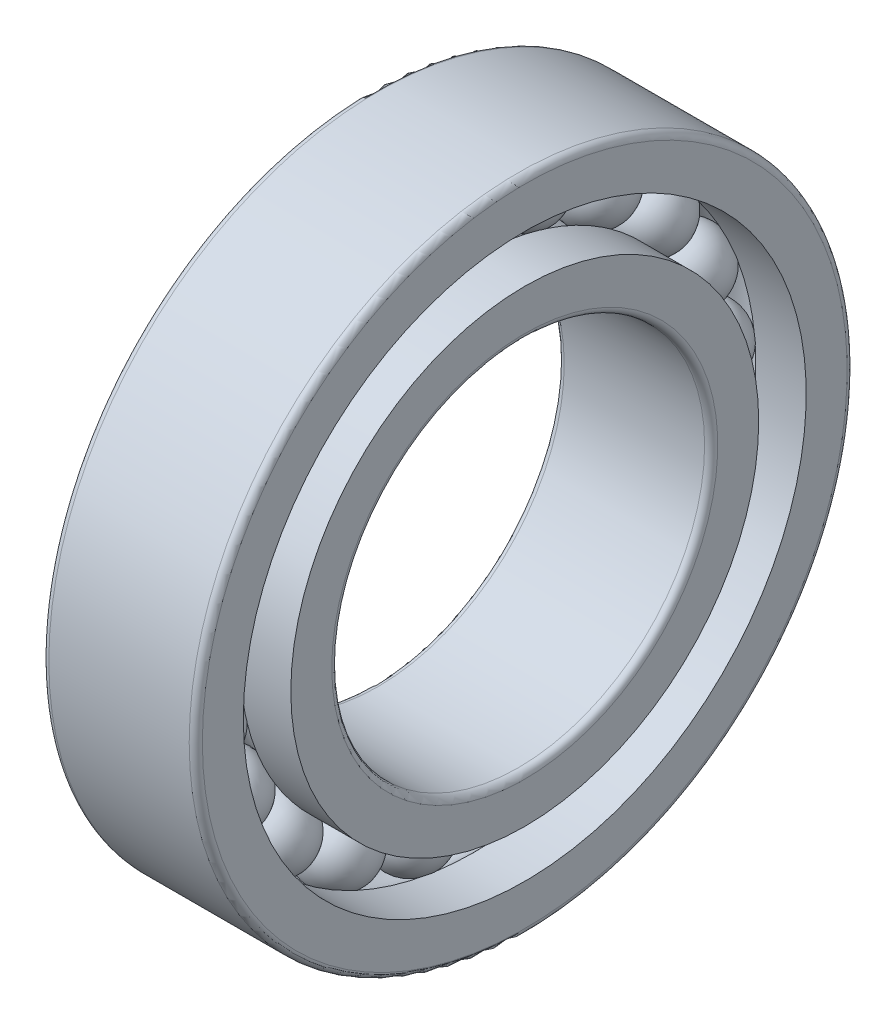
SolidWorks part; units mm, degrees
ref_plane "Front" through (0, 0, 0) normal (0, 0, 1) x (1, 0, 0)
ref_plane "Top" through (0, 0, 0) normal (0, 1, 0) x (1, 0, 0)
ref_plane "Right" through (0, 0, 0) normal (1, 0, 0) x (0, 0, -1)
sketch "Sketch1" plane through (0, 0, 0) normal (0, 0, 1) x (1, 0, 0)
  line L0 (-9.6833, 0) -> (9.8371, 0) construction
  line L1 (-1.625, 11.75) -> (1.625, 11.75)
  line L2 (-4.5966, 11.75) -> (4.6657, 11.75) construction
  arc A0 (1.625, 11.75) -> (-1.625, 11.75) centre (0, 11.75) ccw
revolve "Revolve1" add sketch "Sketch1" angle 360 about L2
sketch "Sketch2" plane through (0, 0, 0) normal (0, 0, 1) x (1, 0, 0)
  line L0 (-3.5, 10.6667) -> (-3.5, 8.5)
  line L1 (-3.5, 8.5) -> (3.5, 8.5)
  line L2 (3.5, 8.5) -> (3.5, 10.6667)
  line L3 (3.5, 10.6667) -> (1.1978, 10.6667)
  line L4 (-6.9714, 0) -> (8.1665, 0) construction
  line L5 (-6.7058, 11.75) -> (6.7058, 11.75) construction
  line L6 (-1.1978, 10.6667) -> (-3.5, 10.6667)
  arc A0 (-1.1978, 10.6667) -> (1.1978, 10.6667) centre (0, 11.75) ccw
revolve "Revolve2" add sketch "Sketch2" angle 360 about L4
sketch "Sketch3" plane through (0, 0, 0) normal (0, 0, 1) x (1, 0, 0)
  line L0 (-8.7107, 0) -> (9.1288, 0) construction
  line L1 (-3.5, 15) -> (3.5, 15)
  line L2 (-3.5, 15) -> (-3.5, 12.8333)
  line L3 (-3.5, 12.8333) -> (-1.1978, 12.8333)
  line L4 (3.5, 15) -> (3.5, 12.8333)
  line L5 (-7.2948, 11.75) -> (7.2948, 11.75) construction
  line L6 (1.1978, 12.8333) -> (3.5, 12.8333)
  arc A0 (1.1978, 12.8333) -> (-1.1978, 12.8333) centre (0, 11.75) ccw
revolve "Revolve3" add sketch "Sketch3" angle 360 about L0
pattern_circular "Circular-Pattern1" count 21 over 360 about axis through (0, 0, 0) along (1, 0, 0) of "Revolve1"
fillet "Fillet1" radius 0.3 4 edges at (-3.5, 0, 8.5) (-3.5, 0, 15) (3.5, 0, 15) (3.5, 0, 8.5)
equation "\"d0@Sketch1\" = ( \"DD@Sketch3\" + \"d@Sketch2\" )  / 2"
equation "\"dia@Sketch1\" =  ( \"DD@Sketch3\" - \"d@Sketch2\" )  / 4"
equation "\"D3@Sketch2\" = ( \"DD@Sketch3\" + \"d@Sketch2\" )  / 2 / 2"
equation "\"D4@Sketch2\" = ( \"DD@Sketch3\" - \"d@Sketch2\" )  / 6"
equation "\"D5@Sketch2\" = \"dia@Sketch1\" - 0.02"
equation "\"B/2@Sketch2\" = \"B@Sketch2\" / 2"
equation "\"D4@Sketch3\" = ( \"DD@Sketch3\" + \"d@Sketch2\" )  / 2 / 2"
equation "\"D5@Sketch3\" = ( \"DD@Sketch3\" - \"d@Sketch2\" )  / 6"
equation "\"B@Sketch3\" = \"B@Sketch2\""
equation "\"B/2@Sketch3\" = \"B@Sketch3\" / 2"
equation "\"D1@Sketch3\" = \"dia@Sketch1\" - 0.02"
equation "\"m@Circular-Pattern1\" = int( 3.14159265 / atn(( \"dia@Sketch1\" / 2) / sqr(( \"DD@Sketch3\" + \"d@Sketch2\" )  / 2 * ( \"DD@Sketch3\" + \"d@Sketch2\" )  / 2/4 - ( \"dia@Sketch1\" / 2) *  ( \"dia@Sketch1\" / 2))))-1"
